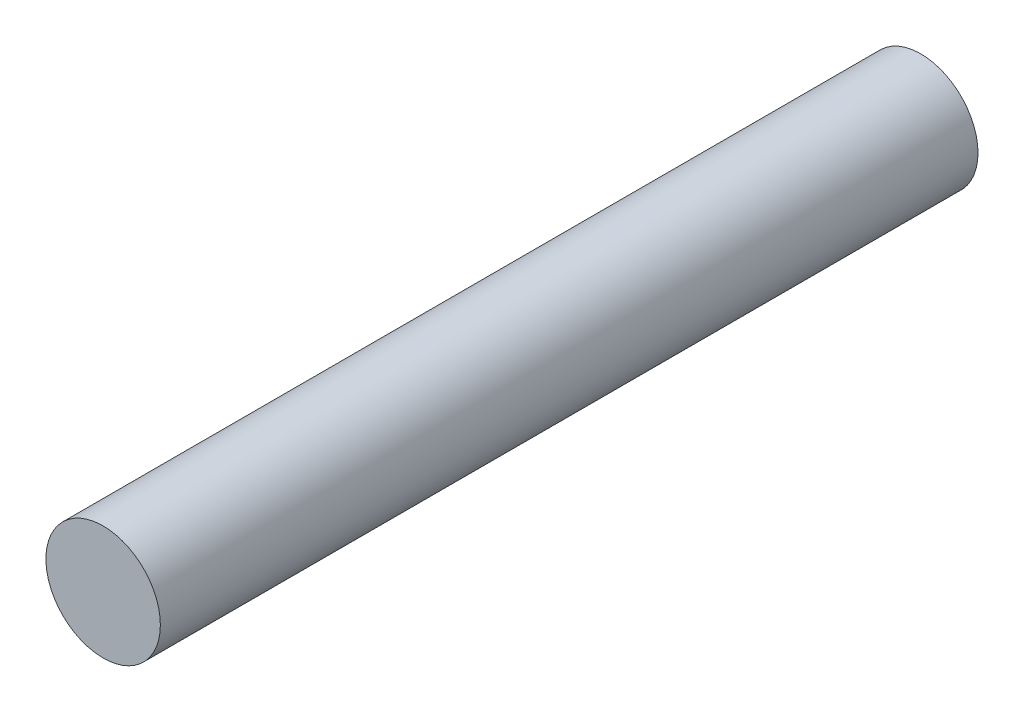
SolidWorks part; units mm, degrees
ref_plane "Front Plane" through (0, 0, 0) normal (0, 0, 1) x (1, 0, 0)
ref_plane "Top Plane" through (0, 0, 0) normal (0, 1, 0) x (1, 0, 0)
ref_plane "Right Plane" through (0, 0, 0) normal (1, 0, 0) x (0, 0, -1)
sketch "Sketch1" plane through (0, 0, 0) normal (0, 0, 1) x (1, 0, 0)
  circle A0 centre (0, 0) radius 3.5
  dimension "D1" = 7
extrude "Boss-Extrude1" add sketch "Sketch1" along normal blind 50
